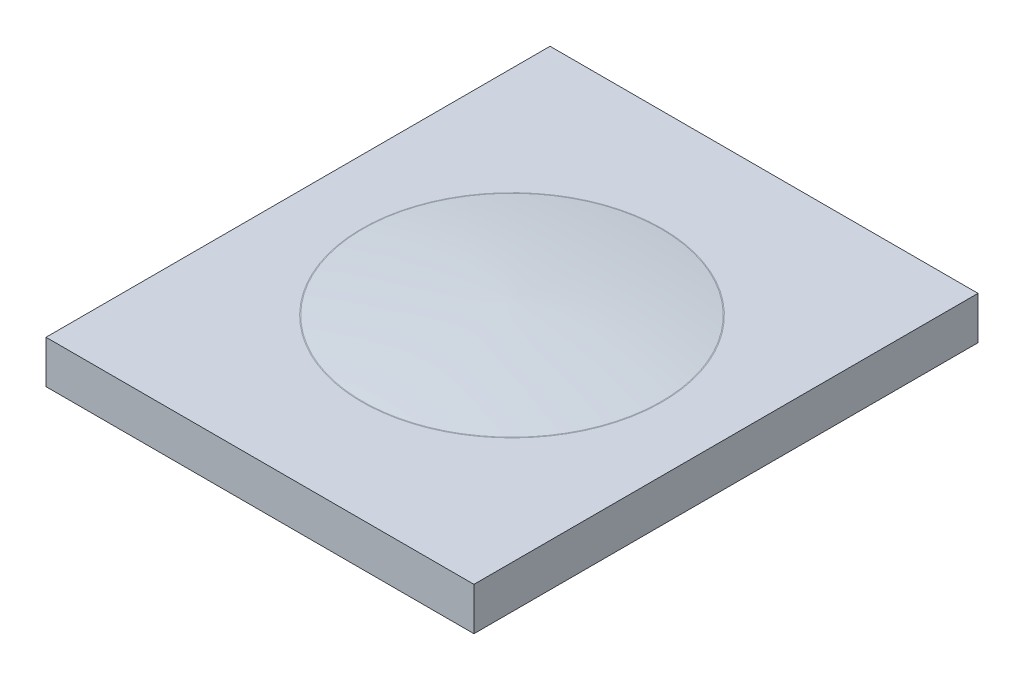
SolidWorks part; units mm, degrees
ref_plane "前视基准面" through (0, 0, 0) normal (0, 0, 1) x (1, 0, 0)
ref_plane "上视基准面" through (0, 0, 0) normal (0, 1, 0) x (1, 0, 0)
ref_plane "右视基准面" through (0, 0, 0) normal (1, 0, 0) x (0, 0, -1)
sketch "草图1" plane through (0, 0, 0) normal (0, 1, 0) x (1, 0, 0)
  line L1 (45, 53) -> (-45, 53)
  line L2 (45, 53) -> (45, -53)
  line L3 (45, -53) -> (-45, -53)
  line L4 (-45, 53) -> (-45, -53)
  line L5 (45, 53) -> (-45, -53) construction
  line L6 (45, -53) -> (-45, 53) construction
  point P0 (0, 0)
  dimension "D1" = 90
  dimension "D2" = 106
extrude "凸台-拉伸1" add sketch "草图1" along normal blind 9
sketch "草图2" plane through (0, 0, 0) normal (0, 0, 1) x (1, 0, 0)
  line L0 (0, 0) -> (0, 30.5125) construction
  line L1 (-45, 9) -> (45, 9) construction
  line L2 (0, 9) -> (31.5, 9)
  line L3 (0, 12.0023) -> (0, 9)
  arc A0 (31.5, 9) -> (0, 12.0023) centre (-7.9224, -237.8722) ccw
  point P6 (15.7975, 11)
  dimension "D1" = 2
  dimension "D3" = 250
  dimension "D2" = 63
revolve "旋转2" add sketch "草图2" angle 360 about L0
fillet "圆角1" radius 1.1 1 edges at (0, 9, -31.5)
sketch "方向草图" plane through (0, 9, 0) normal (0, 1, 0) x (1, 0, 0)
  line L0 (-45, 53) -> (-45, -53) construction
  line L1 (-45, -53) -> (45, -53) construction
  line L2 (45, -53) -> (45, 53) construction
  line L3 (45, 53) -> (-45, 53) construction
  line L4 (-45, 53) -> (-45, -53) construction
  line L5 (-45, -53) -> (45, -53) construction
  line L6 (45, -53) -> (45, 53) construction
  line L7 (45, 53) -> (-45, 53) construction
  circle A0 centre (0, 0) radius 31.5872 construction
  circle A1 centre (0, 0) radius 31.5872
  point P7 (0, 0)
other "成形工具1"
